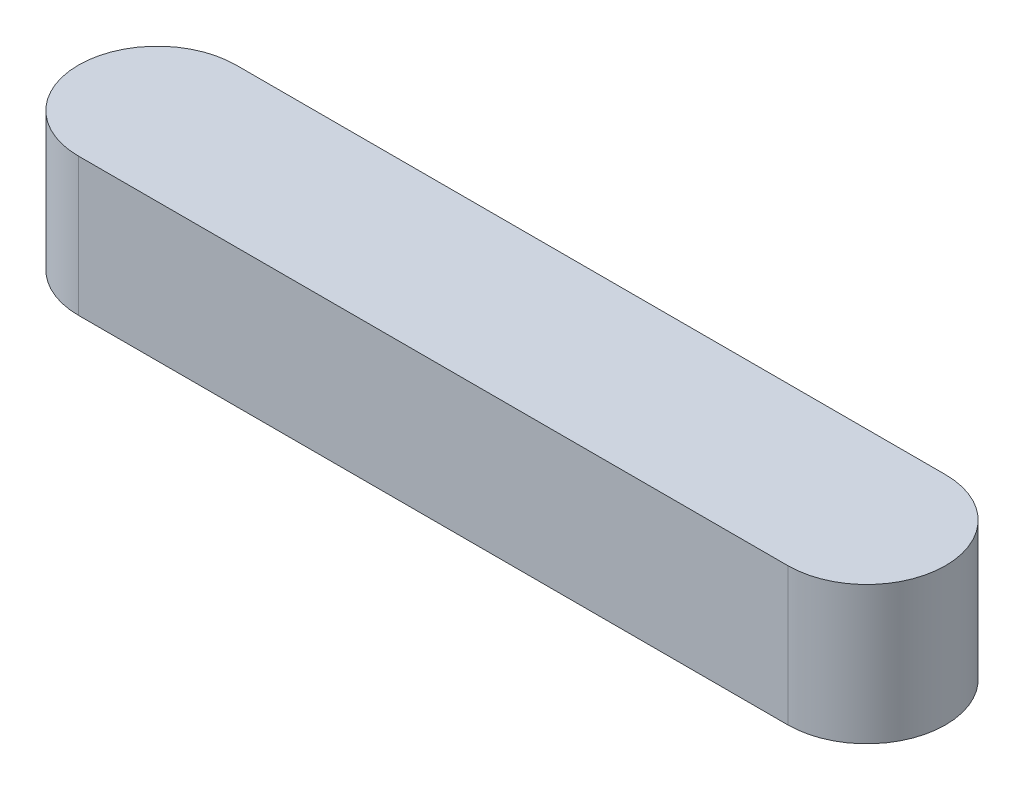
SolidWorks part; units mm, degrees
ref_plane "Front Plane" through (0, 0, 0) normal (0, 0, 1) x (1, 0, 0)
ref_plane "Top Plane" through (0, 0, 0) normal (0, 1, 0) x (1, 0, 0)
ref_plane "Right Plane" through (0, 0, 0) normal (1, 0, 0) x (0, 0, -1)
sketch "Sketch1" plane through (0, 0, 0) normal (0, 1, 0) x (1, 0, 0)
  line L0 (-9, 0) -> (9, 0) construction
  line L1 (-9, 2) -> (9, 2)
  line L2 (-9, -2) -> (9, -2)
  arc A0 (-9, 2) -> (-9, -2) centre (-9, 0) ccw
  arc A1 (9, -2) -> (9, 2) centre (9, 0) ccw
  point P2 (0, 0)
  point P8 (-11, 0)
  point P9 (11, 0)
  dimension "D1" = 22
  dimension "D2" = 4
extrude "Boss-Extrude1" add sketch "Sketch1" along normal blind 3.5
